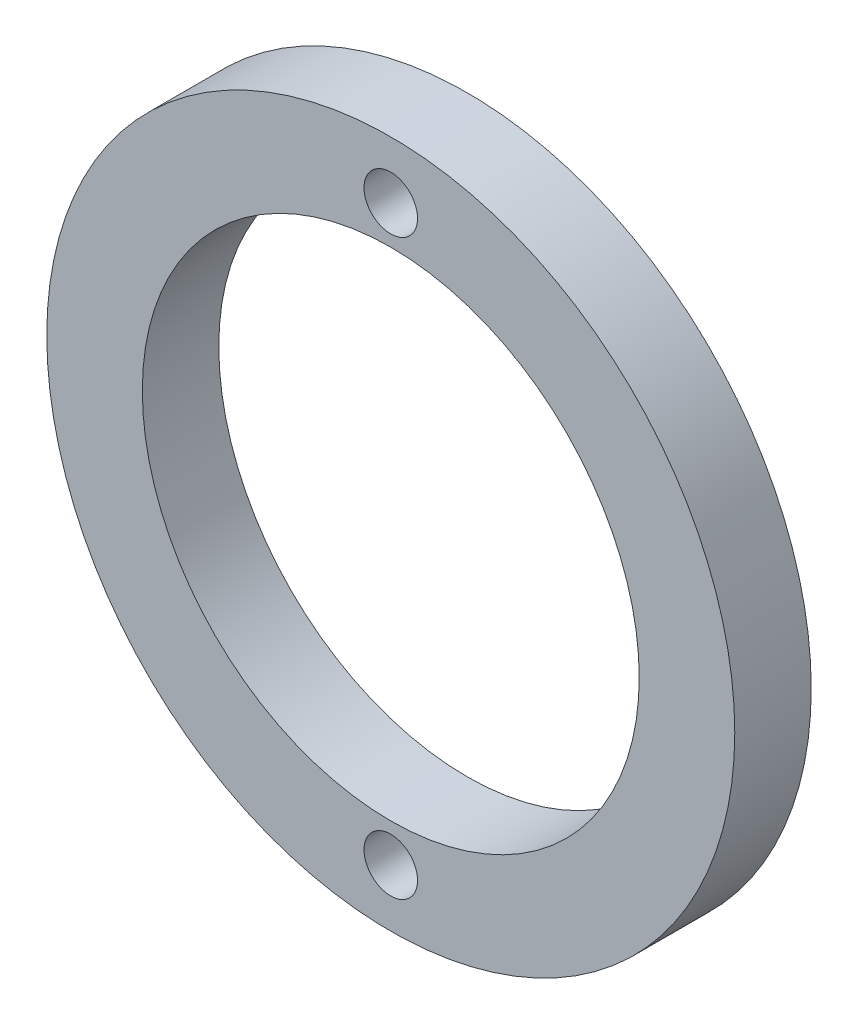
SolidWorks part; units mm, degrees
ref_plane "Front Plane" through (0, 0, 0) normal (0, 0, 1) x (1, 0, 0)
ref_plane "Top Plane" through (0, 0, 0) normal (0, 1, 0) x (1, 0, 0)
ref_plane "Right Plane" through (0, 0, 0) normal (1, 0, 0) x (0, 0, -1)
sketch "Sketch1" plane through (0, 0, 0) normal (0, 0, 1) x (1, 0, 0)
  circle A0 centre (0, 0) radius 11.43
  circle A1 centre (0, 0) radius 8.255
  dimension "D1" = 22.86
  dimension "D2" = 3.175
extrude "Boss-Extrude1" add sketch "Sketch1" along normal blind 2.54
fillet "Fillet1" [suppressed] radius 0.635
hole_wizard "#2-56 Tapped Hole1" positions "Sketch2" profile "Sketch3" tap size "#2-56" standard "ANSI Inch" end condition through all
sketch "Sketch2" plane through (0, 0, 2.54) normal (0, 0, 1) x (1, 0, 0)
  point P0 (0, 9.525)
  dimension "D1" = 9.525
sketch "Sketch3" plane through (0, 9.525, 2.54) normal (1, 0, 0) x (0, -1, 0)
  line L0 (0, 0) -> (0, 2.54)
  line L1 (0, 2.54) -> (0.889, 2.54)
  line L2 (0.889, 2.54) -> (0.889, 0)
  line L5 (0.889, 0) -> (0, 0)
  line L11 (0, -6.35) -> (0, 107.95) construction
  dimension "Thru Tap Drill Dia." = 1.778
  dimension "Thru Tap Drill Depth" = 2.54
cosmetic thread "Hole Thread1" parameters "D2"=2.1844
mirror "Mirror1" about plane through (0, 0, 0) normal (0, 1, 0) of "#2-56 Tapped Hole1"
